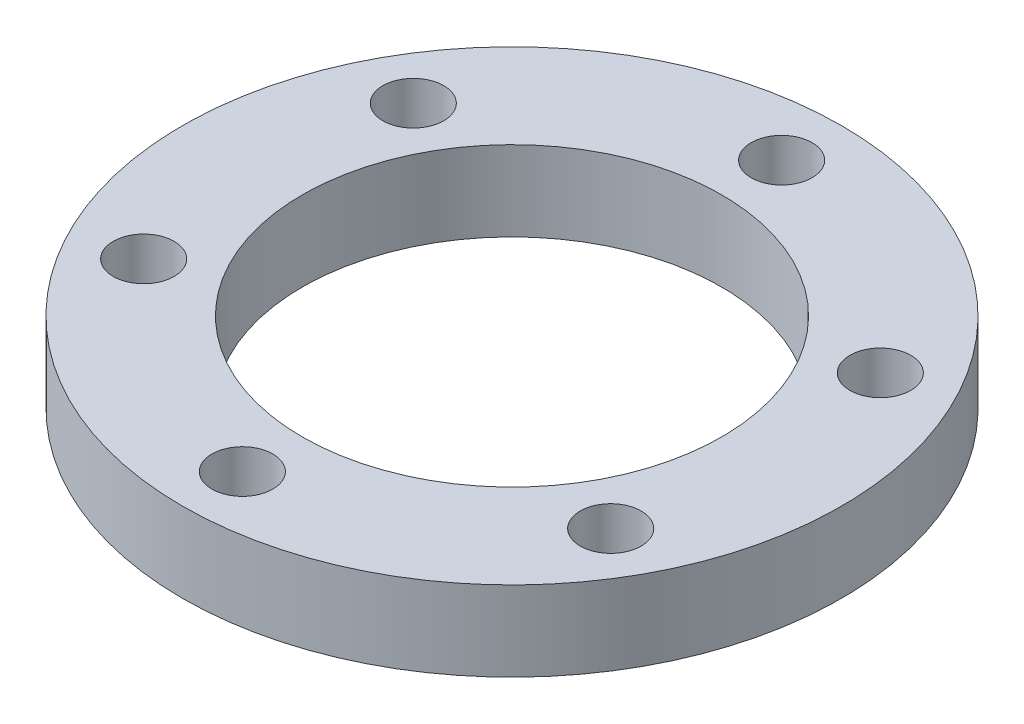
SolidWorks part; units mm, degrees
material "Thornel Mat VMA"
ref_plane "前视基准面" through (0, 0, 0) normal (0, 0, 1) x (1, 0, 0)
ref_plane "上视基准面" through (0, 0, 0) normal (0, 1, 0) x (1, 0, 0)
ref_plane "右视基准面" through (0, 0, 0) normal (1, 0, 0) x (0, 0, -1)
sketch "草图1" plane through (0, 0, 0) normal (0, 1, 0) x (1, 0, 0)
  circle A0 centre (0, 0) radius 13.5 construction
  circle A1 centre (0, 13.5) radius 1.525
  circle A2 centre (11.6913, 6.75) radius 1.525
  circle A3 centre (11.6913, -6.75) radius 1.525
  circle A4 centre (0, -13.5) radius 1.525
  circle A5 centre (-11.6913, -6.75) radius 1.525
  circle A6 centre (-11.6913, 6.75) radius 1.525
  circle A7 centre (0, 0) radius 10.5
  circle A8 centre (0, 0) radius 16.5
  point P17 (0, 0)
  dimension "D1" = 27
  dimension "D2" = 3.05
  dimension "D4" = 3
  dimension "D5" = 3
  dimension "D3" = 6
extrude "凸台-拉伸1" add sketch "草图1" along normal blind 4
